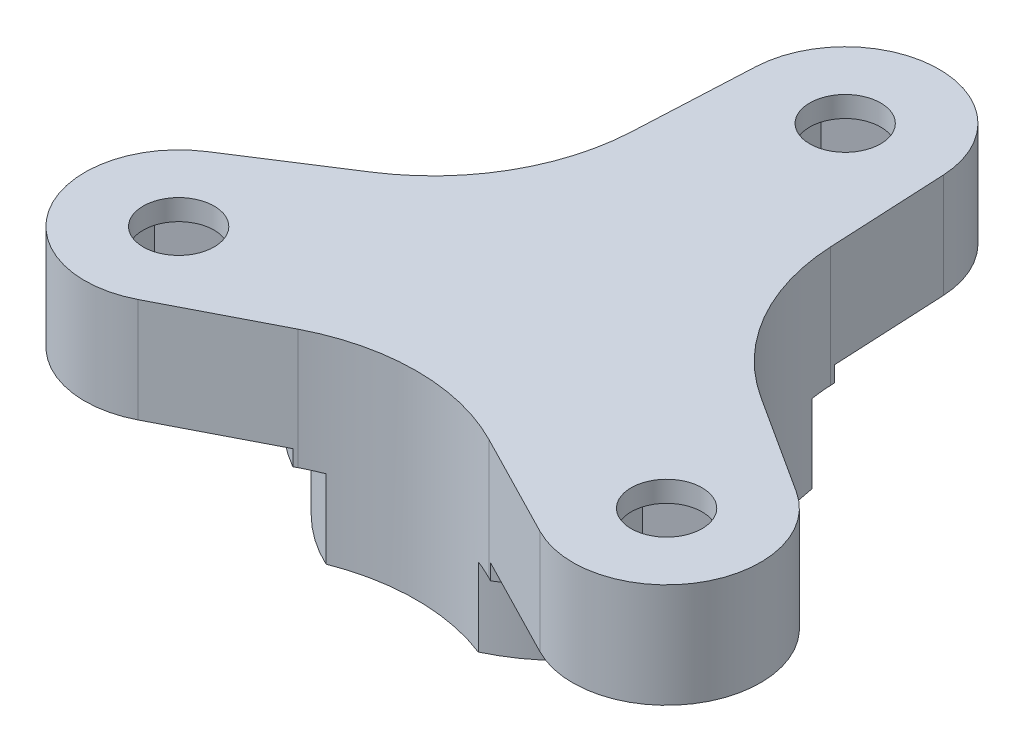
SolidWorks part; units mm, degrees
ref_plane "Ön Düzlem" through (0, 0, 0) normal (0, 0, 1) x (1, 0, 0)
ref_plane "Üst Düzlem" through (0, 0, 0) normal (0, 1, 0) x (1, 0, 0)
ref_plane "Sağ Düzlem" through (0, 0, 0) normal (1, 0, 0) x (0, 0, -1)
sketch "Sketch1" plane through (0, 0, 0) normal (0, 1, 0) x (1, 0, 0)
  line L0 (-4.4946, 13.7195) -> (-4.7723, 8.0342)
  line L1 (0, 13.5) -> (0, 0) construction
  line L2 (4.4946, 13.7195) -> (4.7723, 8.0342)
  line L3 (9.6341, -10.7522) -> (4.5717, -8.15)
  line L4 (14.1287, -2.9673) -> (9.3439, 0.1158)
  line L5 (-14.1287, -2.9673) -> (-9.3439, 0.1158)
  line L6 (-9.6341, -10.7522) -> (-4.5717, -8.15)
  circle A1 centre (0, 13.5) radius 1.7
  arc A3 (4.4946, 13.7195) -> (-4.4946, 13.7195) centre (0, 13.5) ccw
  circle A5 centre (0, 13.5) radius 4.5 construction
  circle A6 centre (11.6913, -6.75) radius 1.7
  arc A7 (9.6341, -10.7522) -> (14.1287, -2.9673) centre (11.6913, -6.75) ccw
  circle A8 centre (-11.6913, -6.75) radius 1.7
  arc A9 (-14.1287, -2.9673) -> (-9.6341, -10.7522) centre (-11.6913, -6.75) ccw
  circle A10 centre (0, 0) radius 5.8 construction
  arc A11 (-4.5717, -8.15) -> (4.5717, -8.15) centre (0, -17.0438) cw
  arc A12 (9.3439, 0.1158) -> (4.7723, 8.0342) centre (14.7604, 8.5219) cw
  arc A13 (-4.7723, 8.0342) -> (-9.3439, 0.1158) centre (-14.7604, 8.5219) cw
  point P27 (5.0229, 2.9)
  point P30 (0, 0)
  point P32 (-5.0229, 2.9)
  dimension "D2" = 3.4
  dimension "D3" = 11.6
  dimension "D7" = 10
  dimension "D4" = 4.5
  dimension "D1" = 13.5
  dimension "D6" = 3
extrude "Boss-Extrude1" add sketch "Sketch1" along normal blind 5
sketch "Sketch2" plane through (0, 5, 0) normal (0, 1, 0) x (1, 0, 0)
  line L0 (14.4413, -8.3377) -> (14.4413, -5.1623)
  line L1 (0, 16.6754) -> (-2.75, 15.0877)
  line L2 (-2.75, 15.0877) -> (-2.75, 11.9123)
  line L3 (-2.75, 11.9123) -> (0, 10.3246)
  line L4 (0, 10.3246) -> (2.75, 11.9123)
  line L5 (2.75, 11.9123) -> (2.75, 15.0877)
  line L6 (2.75, 15.0877) -> (0, 16.6754)
  line L7 (14.4413, -5.1623) -> (11.6913, -3.5746)
  line L8 (11.6913, -3.5746) -> (8.9413, -5.1623)
  line L9 (8.9413, -5.1623) -> (8.9413, -8.3377)
  line L10 (8.9413, -8.3377) -> (11.6913, -9.9254)
  line L11 (11.6913, -9.9254) -> (14.4413, -8.3377)
  line L12 (-14.4413, -8.3377) -> (-11.6913, -9.9254)
  line L13 (-11.6913, -9.9254) -> (-8.9413, -8.3377)
  line L14 (-8.9413, -8.3377) -> (-8.9413, -5.1623)
  line L15 (-8.9413, -5.1623) -> (-11.6913, -3.5746)
  line L16 (-11.6913, -3.5746) -> (-14.4413, -5.1623)
  line L17 (-14.4413, -5.1623) -> (-14.4413, -8.3377)
  circle A0 centre (0, 13.5) radius 2.75 construction
  point P24 (0, 0)
  dimension "D1" = 5.5
  dimension "D2" = 3
extrude "Cut-Extrude1" cut sketch "Sketch2" along normal blind 4 from surface at -5 starting at face at (0, 0, 0)
sketch "Sketch7" plane through (0, 0, 0) normal (0, -1, 0) x (1, 0, 0)
  arc A0 (-4.873, -7.0254) -> (4.873, -7.0254) centre (0, 0) ccw
  arc A1 (-4.7723, -8.0342) -> (-9.3439, -0.1158) centre (-14.7604, -8.5219) ccw construction
  arc A2 (9.3439, -0.1158) -> (4.7723, -8.0342) centre (14.7604, -8.5219) ccw construction
  arc A3 (-4.5717, 8.15) -> (4.5717, 8.15) centre (0, 17.0438) ccw construction
  arc A4 (-4.873, -7.0254) -> (-8.5207, -0.7074) centre (-14.7604, -8.5219) ccw
  arc A5 (8.5207, -0.7074) -> (4.873, -7.0254) centre (14.7604, -8.5219) ccw
  arc A6 (-3.6477, 7.7328) -> (3.6477, 7.7328) centre (0, 17.0438) ccw
  arc A7 (8.5207, -0.7074) -> (3.6477, 7.7328) centre (0, 0) ccw
  arc A8 (-3.6477, 7.7328) -> (-8.5207, -0.7074) centre (0, 0) ccw
  dimension "D1" = 17.1
extrude "Boss-Extrude3" add sketch "Sketch7" along normal blind 4.5
sketch "Sketch8" plane through (0, 0, 0) normal (0, -1, 0) x (1, 0, 0)
  line L0 (-9.3439, -0.1158) -> (-14.1287, 2.9673) construction
  line L1 (-9.6341, 10.7522) -> (-4.5717, 8.15) construction
  line L2 (-9.3439, -0.1158) -> (-9.5, -0.0152)
  line L3 (-4.7368, 8.2349) -> (-4.5717, 8.15)
  line L4 (4.5717, 8.15) -> (4.7368, 8.2349)
  line L5 (9.5, -0.0152) -> (9.3439, -0.1158)
  line L6 (4.7723, -8.0342) -> (4.7632, -8.2196)
  line L7 (-4.7632, -8.2196) -> (-4.7723, -8.0342)
  arc A0 (-4.7368, 8.2349) -> (-9.5, -0.0152) centre (0, 0) ccw
  arc A1 (-8.5207, -0.7074) -> (-9.3439, -0.1158) centre (-14.7604, -8.5219) ccw construction
  arc A2 (-4.5717, 8.15) -> (-3.6477, 7.7328) centre (0, 17.0438) ccw construction
  arc A3 (-3.6477, 7.7328) -> (-8.5207, -0.7074) centre (0, 0) ccw construction
  arc A4 (-8.5207, -0.7074) -> (-9.3439, -0.1158) centre (-14.7604, -8.5219) ccw
  arc A5 (-4.5717, 8.15) -> (-3.6477, 7.7328) centre (0, 17.0438) ccw
  arc A6 (-3.6477, 7.7328) -> (-8.5207, -0.7074) centre (0, 0) ccw
  arc A7 (9.5, -0.0152) -> (4.7368, 8.2349) centre (0, 0) ccw
  arc A8 (3.6477, 7.7328) -> (4.5717, 8.15) centre (0, 17.0438) ccw
  arc A9 (8.5207, -0.7074) -> (3.6477, 7.7328) centre (0, 0) ccw
  arc A10 (9.3439, -0.1158) -> (8.5207, -0.7074) centre (14.7604, -8.5219) ccw
  arc A11 (-4.7632, -8.2196) -> (4.7632, -8.2196) centre (0, 0) ccw
  arc A12 (4.873, -7.0254) -> (4.7723, -8.0342) centre (14.7604, -8.5219) ccw
  arc A13 (-4.873, -7.0254) -> (4.873, -7.0254) centre (0, 0) ccw
  arc A14 (-4.7723, -8.0342) -> (-4.873, -7.0254) centre (-14.7604, -8.5219) ccw
  point P30 (0, 0)
  dimension "D1" = 9.5
  dimension "D2" = 3
extrude "Boss-Extrude4" add sketch "Sketch8" along normal blind 0.75
